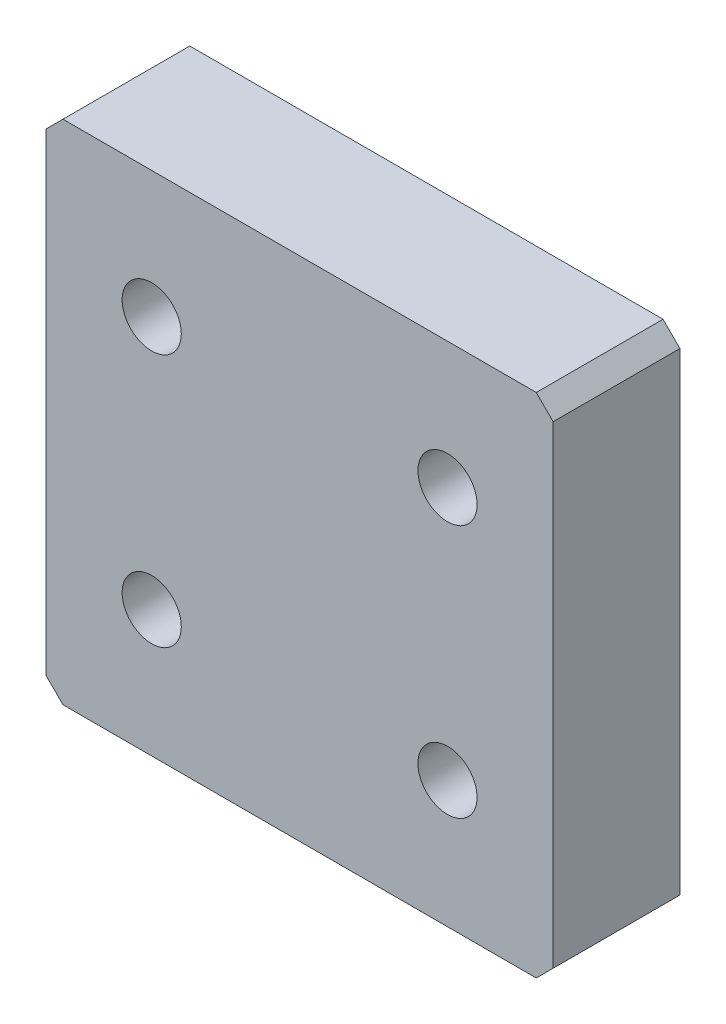
SolidWorks part; units mm, degrees
ref_plane "Front Plane" through (0, 0, 0) normal (0, 0, 1) x (1, 0, 0)
ref_plane "Top Plane" through (0, 0, 0) normal (0, 1, 0) x (1, 0, 0)
ref_plane "Right Plane" through (0, 0, 0) normal (1, 0, 0) x (0, 0, -1)
sketch "Sketch1" plane through (0, 0, 0) normal (0, 0, 1) x (1, 0, 0)
  line L1 (-30, 30) -> (30, 30)
  line L2 (-30, 30) -> (-30, -30)
  line L3 (-30, -30) -> (30, -30)
  line L4 (30, 30) -> (30, -30)
  line L5 (-30, 30) -> (30, -30) construction
  line L6 (-30, -30) -> (30, 30) construction
  circle A0 centre (-17.5, 15) radius 3.5
  circle A1 centre (17.5, 15) radius 3.5
  circle A2 centre (-17.5, -15) radius 3.5
  circle A3 centre (17.5, -15) radius 3.5
  point P0 (0, 0)
  point P14 (0, 0)
  point P15 (0, 0)
  point P16 (0, 0)
  point P17 (0, 0)
  dimension "D3" = 7
  dimension "D1" = 60
  dimension "D2" = 60
  dimension "D4" = 15
  dimension "D5" = 30
  dimension "D6" = 12.5
  dimension "D7" = 12.5
extrude "Boss-Extrude1" add sketch "Sketch1" along normal blind 15
chamfer "Chamfer1" distance 2 angle 45 4 edges at (30, 30, 7.5) (-30, 30, 7.5) (-30, -30, 7.5) (30, -30, 7.5)
